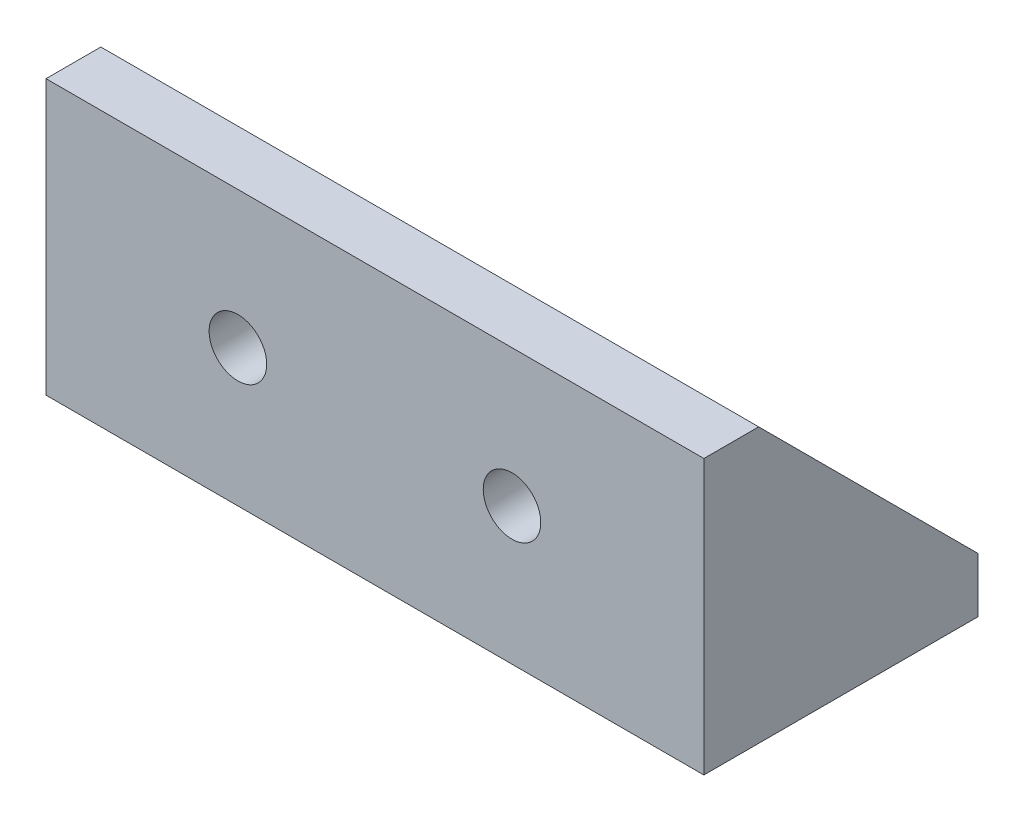
SolidWorks part; units mm, degrees
material "1060 Alloy"
ref_plane "Front Plane" through (0, 0, 0) normal (0, 0, 1) x (1, 0, 0)
ref_plane "Top Plane" through (0, 0, 0) normal (0, 1, 0) x (1, 0, 0)
ref_plane "Right Plane" through (0, 0, 0) normal (1, 0, 0) x (0, 0, -1)
sketch "Sketch1" plane through (0, 0, 0) normal (0, 1, 0) x (1, 0, 0)
  line L1 (0, 0) -> (40, 0)
  line L2 (0, 0) -> (0, 20)
  line L3 (0, 20) -> (40, 20)
  line L4 (40, 0) -> (40, 20)
  dimension "D1" = 40
  dimension "D2" = 20
extrude "Boss-Extrude1" add sketch "Sketch1" along normal blind 4 contours L3 L4 L1 L2
sketch "Sketch2" plane through (0, 4, 0) normal (0, 1, 0) x (1, 0, 0)
  line L0 (20, 20) -> (0, 0) construction
  line L1 (0, 20) -> (40, 20) construction
  line L2 (20, 20) -> (40, 0) construction
  line L3 (0, 20) -> (20, 0) construction
  line L4 (0, 0) -> (40, 0) construction
  line L5 (20, 0) -> (40, 20) construction
  circle A0 centre (10, 10) radius 2.1
  circle A1 centre (30, 10) radius 2.1
  dimension "D1" = 4.2
  dimension "D2" = 4.2
extrude "Cut-Extrude1" cut sketch "Sketch2" against normal blind 4
sketch "Sketch3" plane through (0, 0, 0) normal (0, 0, 1) x (1, 0, 0)
  line L0 (40, 4) -> (40, 0) construction
  line L1 (0, 0) -> (40, 0)
  line L2 (0, 0) -> (0, 20)
  line L3 (0, 20) -> (40, 20)
  line L4 (40, 0) -> (40, 20)
  dimension "D1" = 20
extrude "Boss-Extrude3" add sketch "Sketch3" against normal blind 4 contours L2 L1 L4 L3
sketch "Sketch4" plane through (0, 0, -4) normal (0, 0, -1) x (-1, 0, 0)
  line L0 (-40, 20) -> (-20, 0) construction
  line L1 (0, 0) -> (-40, 0) construction
  line L2 (-20, 0) -> (0, 20) construction
  line L3 (-40, 0) -> (-20, 20) construction
  line L4 (0, 20) -> (-40, 20) construction
  line L5 (-20, 20) -> (0, 0) construction
  circle A0 centre (-30, 10) radius 2.1
  circle A1 centre (-10, 10) radius 2.1
  dimension "D1" = 4.2
  dimension "D2" = 4.2
extrude "Cut-Extrude2" cut sketch "Sketch4" against normal blind 4
sketch "Sketch5" plane through (0, 0, 0) normal (-1, 0, 0) x (0, 0, 1)
  line L0 (-20, 4) -> (-4, 20)
  line L1 (-4, 20) -> (0, 20)
  line L2 (0, 20) -> (0, 0)
  line L3 (0, 0) -> (-20, 0)
  line L4 (-20, 0) -> (-20, 4)
extrude "Boss-Extrude4" add sketch "Sketch5" along normal blind 4
sketch "Sketch6" plane through (40, 0, 0) normal (1, 0, 0) x (0, 0, -1)
  line L0 (0, 20) -> (4, 20)
  line L1 (4, 20) -> (20, 4)
  line L2 (20, 4) -> (20, 0)
  line L3 (20, 0) -> (0, 0)
  line L4 (0, 0) -> (0, 20)
extrude "Boss-Extrude5" add sketch "Sketch6" along normal blind 4
chamfer "Chamfer1" distance 1 angle 45 4 edges at (7.9, 10, -4) (27.9, 10, -4) (30, 4, -7.9) (10, 4, -7.9)
equation "\"tnut_length\"= 16"
equation "\"length\"= \"tnut_length\"*2"
equation "\"height\"= 20"
equation "\"width\"= 4"
equation "\"D1@Sketch1\"=\"length\""
equation "\"D2@Sketch1\"=\"height\""
equation "\"hole_dia\"= 4.2"
equation "\"tnut_length\"= 9.55"
equation "\"length\"= 40"
equation "\"D1@Boss-Extrude1\"=\"width\""
equation "\"D1@Sketch2\"=\"hole_dia\""
equation "\"D2@Sketch2\"=\"hole_dia\""
equation "\"D1@Cut-Extrude1\"=\"width\""
equation "\"D1@Sketch3\"=\"height\""
equation "\"D2@Boss-Extrude3\"=\"width\""
equation "\"D1@Boss-Extrude3\"=\"width\""
equation "\"D1@Sketch4\"= \"hole_dia\""
equation "\"D2@Sketch4\"=\"hole_dia\""
equation "\"D1@Cut-Extrude2\"=\"width\""
equation "\"D1@Boss-Extrude4\"=\"width\""
equation "\"D1@Boss-Extrude5\"=\"width\""
